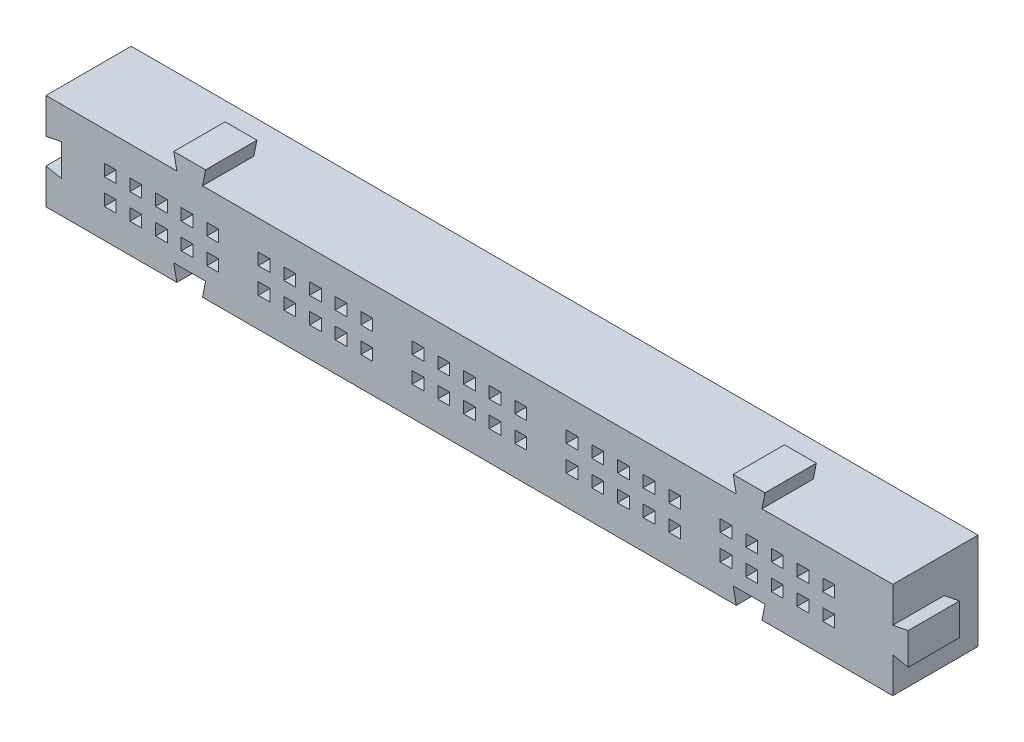
SolidWorks part; units mm, degrees
material "PE hochdicht"
ref_plane "Ebene vorne" through (0, 0, 0) normal (0, 0, 1) x (1, 0, 0)
ref_plane "Ebene oben" through (0, 0, 0) normal (0, 1, 0) x (1, 0, 0)
ref_plane "Ebene rechts" through (0, 0, 0) normal (1, 0, 0) x (0, 0, -1)
sketch "Skizze1" plane through (0, 0, 0) normal (0, 0, 1) x (1, 0, 0)
  line L1 (41.25, -4.7) -> (-41.25, -4.7)
  line L2 (41.25, -4.7) -> (41.25, 4.7)
  line L3 (41.25, 4.7) -> (-41.25, 4.7)
  line L4 (-41.25, -4.7) -> (-41.25, 4.7)
  line L5 (41.25, -4.7) -> (-41.25, 4.7) construction
  line L6 (41.25, 4.7) -> (-41.25, -4.7) construction
  point P0 (0, 0)
  dimension "D1" = 9.4
  dimension "D2" = 82.5
extrude "Aufsatz-Linear austragen1" add sketch "Skizze1" along normal blind 8.3
sketch "Skizze2" plane through (0, 0, 0) normal (0, 0, -1) x (-1, 0, 0)
  line L0 (-34, -0.25) -> (-36, -0.25)
  line L1 (-34, -0.25) -> (-34, -2.25)
  line L2 (-34, -2.25) -> (-36, -2.25)
  line L3 (-36, -0.25) -> (-36, -2.25)
  line L4 (-34, -0.25) -> (-36, -2.25) construction
  line L5 (-34, -2.25) -> (-36, -0.25) construction
  line L6 (-41.25, -4.7) -> (-41.25, 4.7) construction
  line L7 (41.25, -4.7) -> (-41.25, -4.7) construction
  line L8 (-19, -0.25) -> (-21, -0.25)
  line L9 (-19, -0.25) -> (-19, -2.25)
  line L10 (-19, -2.25) -> (-21, -2.25)
  line L11 (-21, -0.25) -> (-21, -2.25)
  line L12 (-19, -0.25) -> (-21, -2.25) construction
  line L13 (-19, -2.25) -> (-21, -0.25) construction
  line L14 (-4, -0.25) -> (-6, -0.25)
  line L15 (-4, -0.25) -> (-4, -2.25)
  line L16 (-4, -2.25) -> (-6, -2.25)
  line L17 (-6, -0.25) -> (-6, -2.25)
  line L18 (-4, -0.25) -> (-6, -2.25) construction
  line L19 (-4, -2.25) -> (-6, -0.25) construction
  line L20 (11, -0.25) -> (9, -0.25)
  line L21 (11, -0.25) -> (11, -2.25)
  line L22 (11, -2.25) -> (9, -2.25)
  line L23 (9, -0.25) -> (9, -2.25)
  line L24 (11, -0.25) -> (9, -2.25) construction
  line L25 (11, -2.25) -> (9, -0.25) construction
  line L26 (26, -0.25) -> (24, -0.25)
  line L27 (26, -0.25) -> (26, -2.25)
  line L28 (26, -2.25) -> (24, -2.25)
  line L29 (24, -0.25) -> (24, -2.25)
  line L30 (26, -0.25) -> (24, -2.25) construction
  line L31 (26, -2.25) -> (24, -0.25) construction
  point P0 (-35, -1.25)
  point P9 (-20, -1.25)
  point P14 (-5, -1.25)
  point P19 (10, -1.25)
  point P24 (25, -1.25)
  dimension "D1" = 2
  dimension "D2" = 2
  dimension "D3" = 6.25
  dimension "D4" = 3.45
  dimension "D5" = 2
  dimension "D6" = 2
  dimension "D7" = 2
  dimension "D8" = 2
  dimension "D9" = 2
  dimension "D10" = 2
  dimension "D11" = 2
  dimension "D12" = 2
  dimension "D13" = 15
  dimension "D14" = 15
  dimension "D15" = 15
  dimension "D16" = 15
extrude "Schnitt-Linear austragen1" cut sketch "Skizze2" against normal blind 2 draft 12
sketch "Skizze3" plane through (0, 0, 2) normal (0, 0, -1) x (-1, 0, 0)
  line L0 (-34.4251, -0.6751) -> (-34, -0.25) construction
  line L1 (-35.5749, -1.8249) -> (-34.4251, -1.8249)
  line L2 (-35.5749, -1.8249) -> (-35.5749, -0.6751)
  line L3 (-35.5749, -0.6751) -> (-34.4251, -0.6751)
  line L4 (-34.4251, -1.8249) -> (-34.4251, -0.6751)
  line L5 (-34.4251, -1.8249) -> (-34.4251, -0.6751) construction
  line L7 (-20.5749, -1.8249) -> (-19.4251, -1.8249)
  line L8 (-20.5749, -1.8249) -> (-20.5749, -0.6751)
  line L9 (-20.5749, -0.6751) -> (-19.4251, -0.6751)
  line L10 (-19.4251, -1.8249) -> (-19.4251, -0.6751)
  line L11 (-5.5749, -1.8249) -> (-4.4251, -1.8249)
  line L12 (-5.5749, -1.8249) -> (-5.5749, -0.6751)
  line L13 (-5.5749, -0.6751) -> (-4.4251, -0.6751)
  line L14 (-4.4251, -1.8249) -> (-4.4251, -0.6751)
  line L15 (9.4251, -1.8249) -> (10.5749, -1.8249)
  line L16 (9.4251, -1.8249) -> (9.4251, -0.6751)
  line L17 (9.4251, -0.6751) -> (10.5749, -0.6751)
  line L18 (10.5749, -1.8249) -> (10.5749, -0.6751)
  line L19 (24.4251, -1.8249) -> (25.5749, -1.8249)
  line L20 (24.4251, -1.8249) -> (24.4251, -0.6751)
  line L21 (24.4251, -0.6751) -> (25.5749, -0.6751)
  line L22 (25.5749, -1.8249) -> (25.5749, -0.6751)
extrude "Schnitt-Linear austragen2" cut sketch "Skizze3" against normal up to next (6.3 mm away)
pattern_linear "Lineares Muster1" count 5 spacing 2.5 along (-1, 0, 0) count 2 spacing 2.5 along (0, 1, 0) of "Schnitt-Linear austragen1", "Schnitt-Linear austragen2"
sketch "Skizze4" plane through (0, 0, 0) normal (0, 0, -1) x (-1, 0, 0)
  line L0 (-26, 4.7) -> (-25.7, 6.2)
  line L1 (-28.5, 4.7) -> (-28.8, 6.2)
  line L2 (-28.8, 6.2) -> (-25.7, 6.2)
  line L3 (-26, 4.7) -> (-28.5, 4.7)
  line L4 (-27.25, 4.7) -> (-27.25, 6.2) construction
  line L5 (-41.25, 4.7) -> (41.25, 4.7) construction
  line L7 (-41.25, -4.7) -> (-41.25, 4.7) construction
  line L8 (28.5, 4.7) -> (28.8, 6.2)
  line L9 (26, 4.7) -> (25.7, 6.2)
  line L10 (25.7, 6.2) -> (28.8, 6.2)
  line L11 (28.5, 4.7) -> (26, 4.7)
  line L12 (27.25, 4.7) -> (27.25, 6.2) construction
  line L13 (41.25, 4.7) -> (41.25, -4.7) construction
  line L14 (-41.25, 1.25) -> (-42.75, 1.55)
  line L15 (-41.25, -1.25) -> (-42.75, -1.55)
  line L16 (-42.75, -1.55) -> (-42.75, 1.55)
  line L17 (-41.25, 1.25) -> (-41.25, -1.25)
  line L18 (-41.25, 0) -> (-42.75, 0) construction
  dimension "D1" = 2.5
  dimension "D2" = 1.5
  dimension "D3" = 14
  dimension "D4" = 3.1
  dimension "D5" = 2.5
  dimension "D6" = 1.5
  dimension "D7" = 3.1
  dimension "D8" = 14
  dimension "D9" = 2.5
  dimension "D10" = 1.5
  dimension "D11" = 3.1
extrude "Aufsatz-Linear austragen2" add sketch "Skizze4" along direction (0, 0, 1) on the side against the normal up to surface (8.3 mm away)
sketch "Skizze5" plane through (0, 0, 0) normal (0, 0, -1) x (-1, 0, 0)
  line L0 (-43.25, -6.7) -> (43.25, -6.7)
  line L1 (-41.25, -4.7) -> (41.25, -4.7)
  line L2 (-41.25, -4.7) -> (-41.25, 4.7)
  line L3 (-41.25, 4.7) -> (41.25, 4.7)
  line L4 (41.25, -4.7) -> (41.25, 4.7)
  line L5 (43.25, -6.7) -> (43.25, 6.7)
  line L6 (-43.25, 6.7) -> (43.25, 6.7)
  line L7 (-43.25, -6.7) -> (-43.25, 6.7)
  dimension "D1" = 2
extrude "Schnitt-Linear austragen3" cut sketch "Skizze5" against normal blind 3.3
sketch "Skizze6" plane through (0, 0, 8.3) normal (0, 0, 1) x (1, 0, 0)
  line L0 (-41.25, -1.25) -> (-39.75, -1.55)
  line L1 (-41.25, 1.25) -> (-39.75, 1.55)
  line L2 (-39.75, 1.55) -> (-39.75, -1.55)
  line L3 (-41.25, -1.25) -> (-41.25, 1.25)
  line L4 (-41.25, 0) -> (-39.75, 0) construction
  line L5 (-41.25, 4.7) -> (-41.25, -4.7) construction
  line L6 (-26, -4.7) -> (-25.7, -3.2)
  line L7 (-28.5, -4.7) -> (-28.8, -3.2)
  line L8 (-28.8, -3.2) -> (-25.7, -3.2)
  line L9 (-26, -4.7) -> (-28.5, -4.7)
  line L10 (-27.25, -4.7) -> (-27.25, -3.2) construction
  line L11 (-41.25, -4.7) -> (41.25, -4.7) construction
  line L12 (28.5, -4.7) -> (28.8, -3.2)
  line L13 (26, -4.7) -> (25.7, -3.2)
  line L14 (25.7, -3.2) -> (28.8, -3.2)
  line L15 (28.5, -4.7) -> (26, -4.7)
  line L16 (27.25, -4.7) -> (27.25, -3.2) construction
  line L17 (41.25, -4.7) -> (41.25, -1.25) construction
  dimension "D1" = 2.5
  dimension "D2" = 1.5
  dimension "D3" = 3.1
  dimension "D4" = 2.5
  dimension "D5" = 1.5
  dimension "D6" = 3.1
  dimension "D7" = 14
  dimension "D8" = 2.5
  dimension "D9" = 1.5
  dimension "D10" = 3.1
  dimension "D11" = 14
extrude "Schnitt-Linear austragen4" cut sketch "Skizze6" against normal blind 4.8
